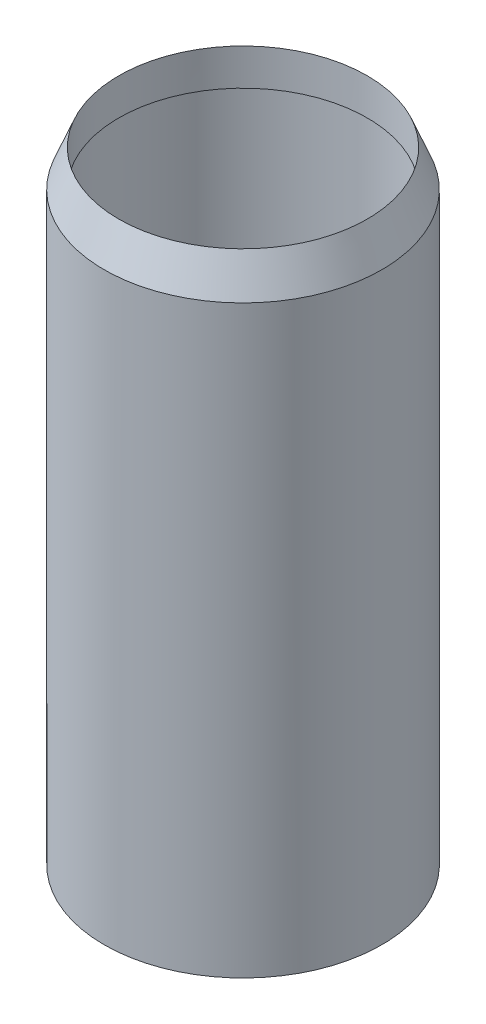
SolidWorks part; units mm, degrees
ref_plane "Спереди" through (0, 0, 0) normal (0, 0, 1) x (1, 0, 0)
ref_plane "Сверху" through (0, 0, 0) normal (0, 1, 0) x (1, 0, 0)
ref_plane "Справа" through (0, 0, 0) normal (1, 0, 0) x (0, 0, -1)
sketch "Эскиз1" plane through (0, 0, 0) normal (0, 1, 0) x (1, 0, 0)
  circle A0 centre (0, 0) radius 17.5
  circle A1 centre (0, 0) radius 19
  dimension "D1" = 35
  dimension "D2" = 38
extrude "Бобышка-Вытянуть1" add sketch "Эскиз1" along normal blind 80
ref_plane "Плоскость1" through (0, 85, 0) normal (0, 1, 0) x (1, 0, 0)
sketch "Эскиз2" plane through (0, 85, 0) normal (0, 1, 0) x (1, 0, 0)
  circle A0 centre (0, 0) radius 17
  dimension "D1" = 34
sketch "Эскиз3" plane through (0, 80, 0) normal (0, 1, 0) x (1, 0, 0)
  circle A0 centre (0, 0) radius 19
loft "По сечениям1" add profiles "Эскиз3", "Эскиз2"
sketch "Эскиз4" plane through (0, 85, 0) normal (0, 1, 0) x (1, 0, 0)
  circle A0 centre (0, 0) radius 17
extrude "Вырез-Вытянуть1" cut sketch "Эскиз4" against normal blind 5
